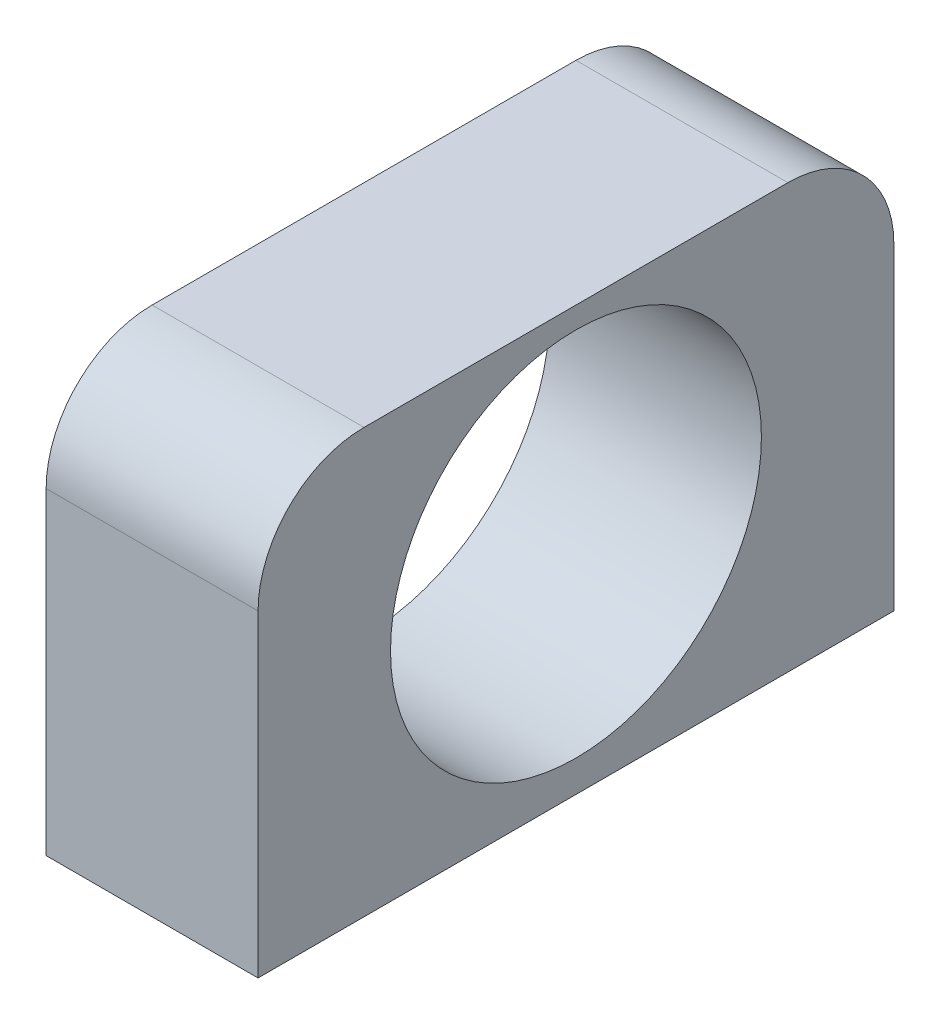
SolidWorks part; units mm, degrees
ref_plane "Front Plane" through (0, 0, 0) normal (0, 0, 1) x (1, 0, 0)
ref_plane "Top Plane" through (0, 0, 0) normal (0, 1, 0) x (1, 0, 0)
ref_plane "Right Plane" through (0, 0, 0) normal (1, 0, 0) x (0, 0, -1)
sketch "Sketch1" plane through (0, 0, 0) normal (0, 1, 0) x (1, 0, 0)
  line L1 (-6.35, -19.05) -> (6.35, -19.05)
  line L2 (-6.35, -19.05) -> (-6.35, 19.05)
  line L3 (-6.35, 19.05) -> (6.35, 19.05)
  line L4 (6.35, -19.05) -> (6.35, 19.05)
  line L5 (-6.35, -19.05) -> (6.35, 19.05) construction
  line L6 (-6.35, 19.05) -> (6.35, -19.05) construction
  point P0 (0, 0)
  dimension "D1" = 12.7
  dimension "D2" = 38.1
extrude "Boss-Extrude1" add sketch "Sketch1" along normal blind 25.4
fillet "Fillet1" radius 6.35 2 edges at (0, 25.4, -19.05) (0, 25.4, 19.05)
sketch "Sketch2" plane through (-6.35, 0, 0) normal (-1, 0, 0) x (0, 0, 1)
  line L0 (-19.05, 0) -> (19.05, 0) construction
  circle A0 centre (0, 13) radius 11.1125
  point P4 (0, 0)
  dimension "D1" = 22.225
  dimension "D2" = 13
extrude "Cut-Extrude1" cut sketch "Sketch2" against normal through all
